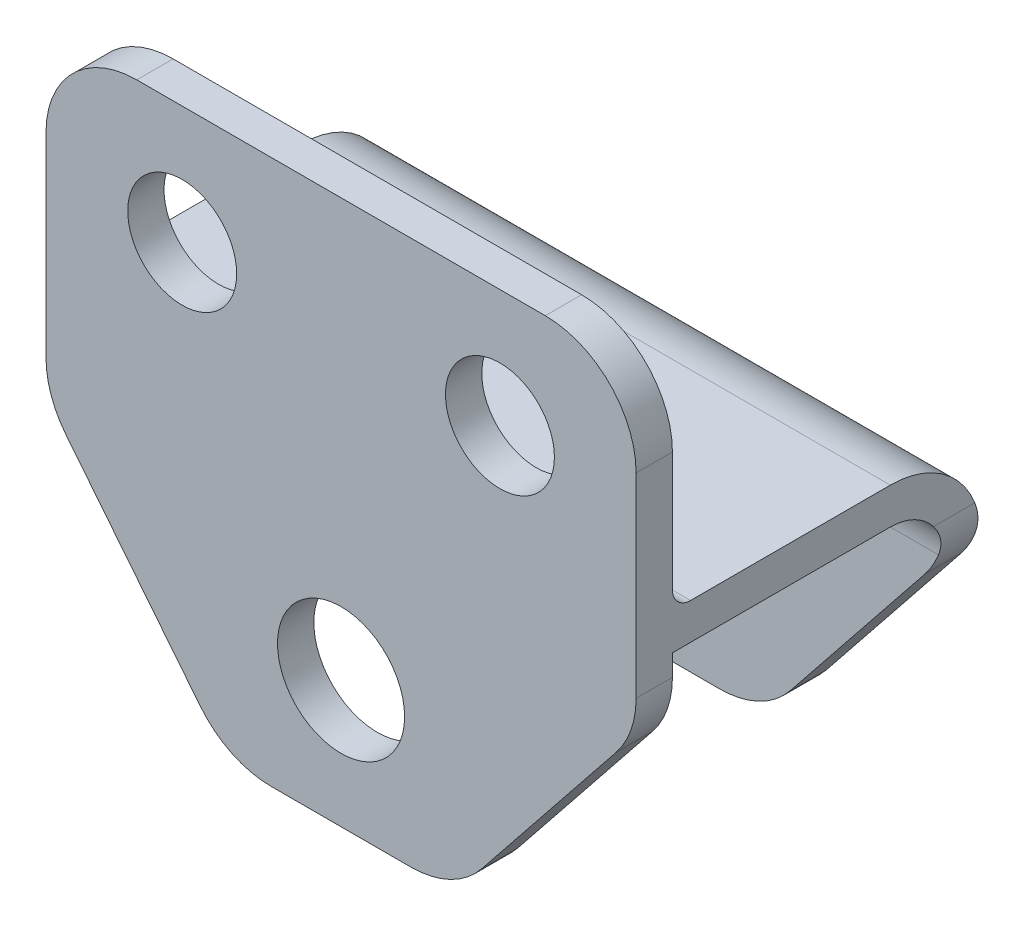
SolidWorks part; units mm, degrees
material "AISI 316 Tôle d'acier inoxydable (SS)"
ref_plane "Plan de face" through (0, 0, 0) normal (0, 0, 1) x (1, 0, 0)
ref_plane "Plan de dessus" through (0, 0, 0) normal (0, 1, 0) x (1, 0, 0)
ref_plane "Plan de droite" through (0, 0, 0) normal (1, 0, 0) x (0, 0, -1)
sketch "Esquisse1" plane through (0, 0, 0) normal (0, 0, 1) x (1, 0, 0)
  line L0 (-32.5, -9.8417) -> (-12.5, -34.8417)
  line L1 (-32.5, 25.1583) -> (32.5, 25.1583)
  line L2 (-32.5, 25.1583) -> (-32.5, -9.8417)
  line L3 (-12.5, -34.8417) -> (12.5, -34.8417)
  line L4 (32.5, 25.1583) -> (32.5, -9.8417)
  line L5 (-17.5, 12.1583) -> (17.5, 12.1583) construction
  line L7 (0, 29.814) -> (0, -35.1859) construction
  line L8 (32.5, -9.8417) -> (12.5, -34.8417)
  circle A0 centre (-17.5, 12.1583) radius 6
  circle A1 centre (17.5, 12.1583) radius 6
  point P0 (0, 0)
  point P1 (0, 12.1583)
  point P18 (0, -20.8417)
  dimension "D1" = 12
  dimension "D2" = 12
  dimension "D3" = 35
  dimension "D5" = 65
  dimension "D6" = 13
  dimension "D7" = 35
  dimension "D8" = 25
  dimension "D10" = 60
extrude "Boss.-Extru.1" add sketch "Esquisse1" along normal blind 4
fillet "Congé1" radius 10 6 edges at (-32.5, 25.1583, 2) (-32.5, -9.8417, 2) (-12.5, -34.8417, 2) (12.5, -34.8417, 2) (32.5, -9.8417, 2) (32.5, 25.1583, 2)
sketch "Esquisse2" plane through (0, 0, 0) normal (1, 0, 0) x (0, 0, -1)
  line L0 (0, 0) -> (24, 0)
  line L1 (0, 15.1583) -> (0, -6.3338) construction
  line L2 (34, -10) -> (34, -35)
  line L3 (0, -4) -> (24, -4)
  line L4 (30, -10) -> (30, -35)
  line L5 (0, 0) -> (0, -4)
  line L6 (34, -35) -> (30, -35)
  arc A0 (24, 0) -> (34, -10) centre (24, -10) cw
  arc A1 (24, -4) -> (30, -10) centre (24, -10) cw
  dimension "D1" = 10
  dimension "D2" = 34
  dimension "D3" = 25
  dimension "D4" = 4
extrude "Boss.-Extru.2" add sketch "Esquisse2" along normal up to surface and the other way up to surface up to face at (32.5, 4.4122, 2) other way up to face at (-32.5, 4.4122, 2)
fillet "Congé2" radius 2 1 edges at (0, 0, 0)
sketch "Esquisse3" plane through (0, 0, -30) normal (0, 0, 1) x (1, 0, 0)
  line L0 (-32.5, -6.3338) -> (-38.6533, -6.3338)
  line L1 (-38.6533, -6.3338) -> (-39.3854, -42.9536)
  line L2 (-39.3854, -42.9536) -> (40.3185, -42.9536)
  line L3 (40.3185, -42.9536) -> (40.3185, -6.3338)
  line L14 (32.5, -6.3338) -> (40.3185, -6.3338)
  line L17 (15.5024, -31.0886) -> (30.3087, -12.5808)
  line L18 (-7.6938, -34.8417) -> (7.6938, -34.8417)
  line L19 (-30.3087, -12.5808) -> (-15.5024, -31.0886)
  line L20 (15.5024, -31.0886) -> (30.3087, -12.5808)
  line L21 (-7.6938, -34.8417) -> (7.6938, -34.8417)
  line L22 (-30.3087, -12.5808) -> (-15.5024, -31.0886)
  arc A14 (30.3087, -12.5808) -> (32.5, -6.3338) centre (22.5, -6.3338) ccw
  arc A15 (7.6938, -34.8417) -> (15.5024, -31.0886) centre (7.6938, -24.8417) ccw
  arc A16 (-15.5024, -31.0886) -> (-7.6938, -34.8417) centre (-7.6938, -24.8417) ccw
  arc A17 (-32.5, -6.3338) -> (-30.3087, -12.5808) centre (-22.5, -6.3338) ccw
  arc A18 (7.6938, -34.8417) -> (15.5024, -31.0886) centre (7.6938, -24.8417) ccw
  arc A19 (-15.5024, -31.0886) -> (-7.6938, -34.8417) centre (-7.6938, -24.8417) ccw
  arc A20 (-32.5, -6.3338) -> (-30.3087, -12.5808) centre (-22.5, -6.3338) ccw
  arc A21 (30.3087, -12.5808) -> (32.5, -6.3338) centre (22.5, -6.3338) ccw
  dimension "D1" = 0
  dimension "D3" = 0
extrude "Enlèv. mat.-Extru.1" cut sketch "Esquisse3" against normal up to next and the other way blind 5
hole_wizard "Diamètre du perçage Ø14.0 (14)1" positions "Esquisse5" profile "Esquisse6" hole size "Ø14.0" standard "Ansi Metric" end condition through all
sketch "Esquisse5" plane through (0, 0, 4) normal (0, 0, 1) x (1, 0, 0)
  point P0 (0, -20.8417)
sketch "Esquisse6" plane through (0, -20.8417, 4) normal (1, 0, 0) x (0, -1, 0)
  line L0 (0, 0) -> (0, 38)
  line L1 (0, 38) -> (7, 38)
  line L2 (7, 38) -> (7, 0)
  line L5 (7, 0) -> (0, 0)
  line L11 (0, -6.35) -> (0, 107.95) construction
  dimension "Diamètre du perçage jusqu'au prochain" = 14
  dimension "Profondeur du perçage jusqu'au prochain" = 38
